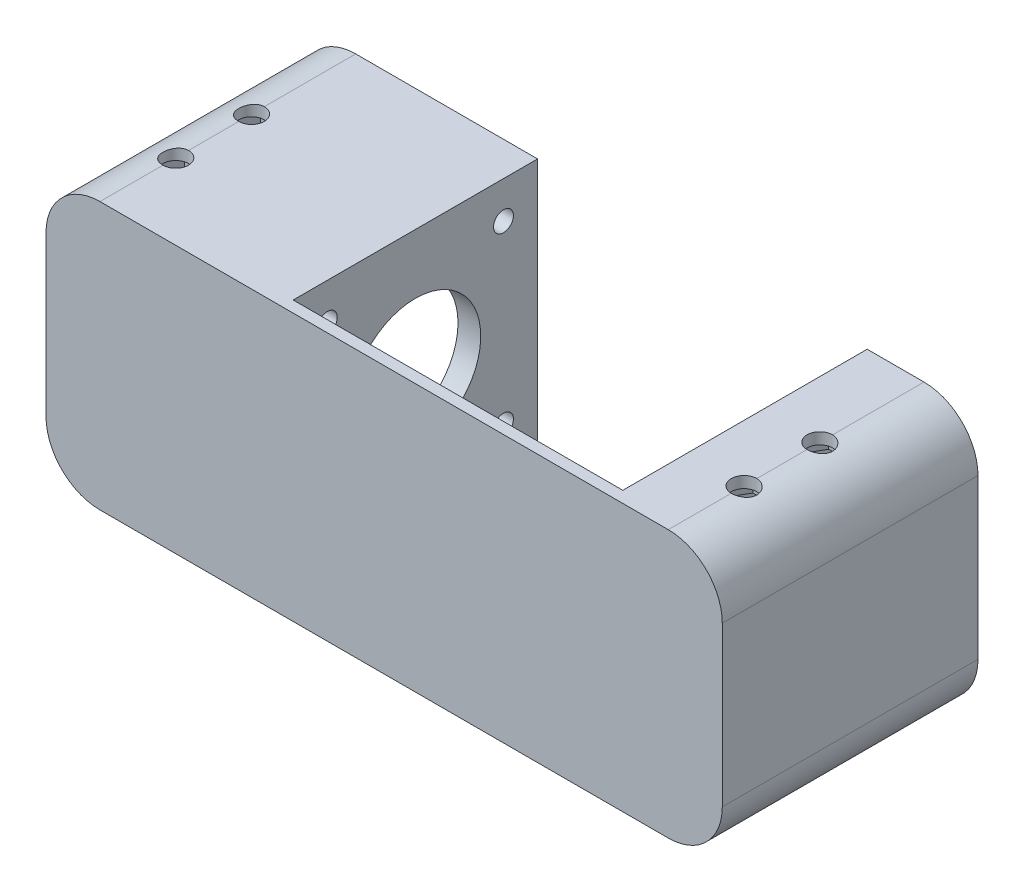
SolidWorks part; units mm, degrees
ref_plane "Front Plane" through (0, 0, 0) normal (0, 0, 1) x (1, 0, 0)
ref_plane "Top Plane" through (0, 0, 0) normal (0, 1, 0) x (1, 0, 0)
ref_plane "Right Plane" through (0, 0, 0) normal (1, 0, 0) x (0, 0, -1)
sketch "Sketch2" plane through (0, 0, 0) normal (0, 0, 1) x (1, 0, 0)
  line L0 (-18, 23.5) -> (-18, -19.5)
  line L1 (-50, -23.5) -> (50, -23.5)
  line L2 (-59.5, -14) -> (-59.5, 14)
  line L3 (-50, 23.5) -> (-18, 23.5)
  line L4 (59.5, -14) -> (59.5, 14)
  line L5 (-59.5, -23.5) -> (59.5, 23.5) construction
  line L6 (-59.5, 23.5) -> (59.5, -23.5) construction
  line L7 (-18, -19.5) -> (35, -19.5)
  line L8 (35, -19.5) -> (35, 23.5)
  line L9 (-50, 19.5) -> (-22, 19.5)
  line L10 (55.5, -14) -> (55.5, 14)
  line L11 (-50, -19.5) -> (-22, -19.5)
  line L12 (-55.5, -14) -> (-55.5, 14)
  line L13 (-22, 19.5) -> (-22, -19.5)
  line L14 (-22, -23.5) -> (39, -23.5)
  line L15 (39, -19.5) -> (39, 19.5)
  line L16 (39, 19.5) -> (50, 19.5)
  line L17 (-22, 23.5) -> (-22, -23.5) construction
  line L18 (35, 23.5) -> (50, 23.5)
  line L19 (-50, 19.5) -> (50, 19.5) construction
  line L20 (39, -19.5) -> (50, -19.5)
  line L21 (-50, 23.5) -> (50, 23.5) construction
  line L22 (39, -23.5) -> (39, 23.5) construction
  line L23 (-18, -19.5) -> (35, -19.5)
  line L24 (-50, -19.5) -> (50, -19.5) construction
  line L25 (-22, -19.5) -> (-22.1358, -19.362)
  arc A0 (-50, -23.5) -> (-59.5, -14) centre (-50, -14) cw
  arc A1 (50, -23.5) -> (59.5, -14) centre (50, -14) ccw
  arc A2 (50, 23.5) -> (59.5, 14) centre (50, 14) cw
  arc A3 (-59.5, 14) -> (-50, 23.5) centre (-50, 14) cw
  arc A4 (50, 19.5) -> (55.5, 14) centre (50, 14) cw
  arc A5 (50, -19.5) -> (55.5, -14) centre (50, -14) ccw
  arc A6 (-50, -19.5) -> (-55.5, -14) centre (-50, -14) cw
  arc A7 (-55.5, 14) -> (-50, 19.5) centre (-50, 14) cw
  point P0 (0, 0)
  dimension "D3" = 9.5
  dimension "D1" = 119
  dimension "D2" = 47
  dimension "D4" = 15
  dimension "D5" = 53
  dimension "D6" = 43
  dimension "D7" = 4
  dimension "D8" = 4
extrude "Boss-Extrude1" add sketch "Sketch2" along normal blind 43 contours A3 L2 A0 L1 A1 L4 A2 L18 L8 L7 L0 L3 A5 L20 L15 L16 A4 L10 L12 A7 L9 L13 L11 A6
sketch "Sketch3" plane through (-18, 0, 0) normal (1, 0, 0) x (0, 0, -1)
  line L0 (-21.5, 23.5) -> (-21.5, -20.5) construction
  line L1 (-43, 23.5) -> (0, 23.5) construction
  line L2 (-21.5, 1.5) -> (-37, 17) construction
  circle A0 centre (-21.5, 1.5) radius 11.5
  circle A1 centre (-37, 17) radius 1.75
  circle A2 centre (-37, -14) radius 1.75
  circle A3 centre (-6, -14) radius 1.75
  circle A4 centre (-6, 17) radius 1.75
  point P17 (-21.5, 1.5)
  dimension "D1" = 23
  dimension "D5" = 3.5
  dimension "D2" = 22
  dimension "D3" = 15.5
  dimension "D4" = 45
  dimension "D6" = 4
extrude "Cut-Extrude1" cut sketch "Sketch3" against normal blind 52
sketch "Sketch4" plane through (0, 0, 43) normal (0, 0, 1) x (1, 0, 0)
  line L0 (-18, 23.5) -> (35, 23.5)
  line L8 (-59.5, 14) -> (-59.5, -14)
  line L9 (-50, -23.5) -> (50, -23.5)
  line L10 (59.5, -14) -> (59.5, 14)
  line L11 (50, 23.5) -> (35, 23.5)
  line L12 (35, 23.5) -> (35, -19.5)
  line L13 (35, -19.5) -> (-18, -19.5)
  line L14 (-18, -19.5) -> (-18, 23.5)
  line L15 (-18, 23.5) -> (-50, 23.5)
  line L16 (-59.5, 14) -> (-59.5, -14)
  line L17 (-50, -23.5) -> (50, -23.5)
  line L18 (59.5, -14) -> (59.5, 14)
  line L19 (50, 23.5) -> (35, 23.5)
  line L23 (-18, 23.5) -> (-50, 23.5)
  arc A4 (-50, 23.5) -> (-59.5, 14) centre (-50, 14) ccw
  arc A5 (-59.5, -14) -> (-50, -23.5) centre (-50, -14) ccw
  arc A6 (50, -23.5) -> (59.5, -14) centre (50, -14) ccw
  arc A7 (59.5, 14) -> (50, 23.5) centre (50, 14) ccw
  arc A8 (-50, 23.5) -> (-59.5, 14) centre (-50, 14) ccw
  arc A9 (-59.5, -14) -> (-50, -23.5) centre (-50, -14) ccw
  arc A10 (50, -23.5) -> (59.5, -14) centre (50, -14) ccw
  arc A11 (59.5, 14) -> (50, 23.5) centre (50, 14) ccw
  dimension "D1" = 0
extrude "Boss-Extrude2" add sketch "Sketch4" along normal blind 2
sketch "Sketch5" plane through (0, 23.5, 0) normal (0, 1, 0) x (1, 0, 0)
  line L0 (-50, -45) -> (-50, -31.6667) construction
  line L1 (-50, -45) -> (-50, 0) construction
  line L2 (-50, -31.6667) -> (-50, -18.3333) construction
  line L3 (-50, -18.3333) -> (-50, -5) construction
  circle A0 centre (-50, -18.3333) radius 2.25
  circle A1 centre (-50, -31.6667) radius 2.25
  dimension "D2" = 4.5
  dimension "D1" = 40
extrude "Cut-Extrude2" cut sketch "Sketch5" against normal blind 50
sketch "Sketch6" plane through (0, -19.5, 0) normal (0, 1, 0) x (1, 0, 0)
  line L1 (-45.7276, -18.3333) -> (-47.8638, -14.6333)
  line L2 (-47.8638, -14.6333) -> (-52.1362, -14.6333)
  line L3 (-52.1362, -14.6333) -> (-54.2724, -18.3333)
  line L4 (-54.2724, -18.3333) -> (-52.1362, -22.0333)
  line L5 (-52.1362, -22.0333) -> (-47.8638, -22.0333)
  line L6 (-47.8638, -22.0333) -> (-45.7276, -18.3333)
  line L7 (-45.7276, -31.6667) -> (-47.8638, -27.9667)
  line L8 (-47.8638, -27.9667) -> (-52.1362, -27.9667)
  line L9 (-52.1362, -27.9667) -> (-54.2724, -31.6667)
  line L10 (-54.2724, -31.6667) -> (-52.1362, -35.3667)
  line L11 (-52.1362, -35.3667) -> (-47.8638, -35.3667)
  line L12 (-47.8638, -35.3667) -> (-45.7276, -31.6667)
  circle A0 centre (-50, -18.3333) radius 3.7 construction
  circle A1 centre (-50, -31.6667) radius 3.7 construction
  dimension "D1" = 7.4
extrude "Cut-Extrude3" cut sketch "Sketch6" against normal blind 2 and the other way blind 2
mirror "Mirror1" about plane through (0, 0, 0) normal (1, 0, 0) of "Cut-Extrude2"
mirror "Mirror2" about plane through (0, 0, 0) normal (0, 1, 0) of "Cut-Extrude3"
mirror "Mirror3" about plane through (0, 0, 0) normal (1, 0, 0) of "Mirror2", "Cut-Extrude3"
sketch "Sketch7" plane through (-59.5, 0, 0) normal (-1, 0, 0) x (0, 0, 1)
  line L0 (14.6333, 19.5) -> (0, 19.5) construction
  circle A0 centre (6, 17) radius 2.5
  circle A1 centre (37, 17) radius 2.5
  circle A2 centre (37, -14) radius 2.5
  circle A3 centre (6, -14) radius 2.5
extrude "Cut-Extrude4" cut sketch "Sketch7" against normal blind 19
chamfer "Chamfer1" distance 5 angle 45 4 edges at (35, 23.5, 21.5) (39, 19.5, 21.5) (39, -19.5, 21.5) (35, -19.5, 21.5)
